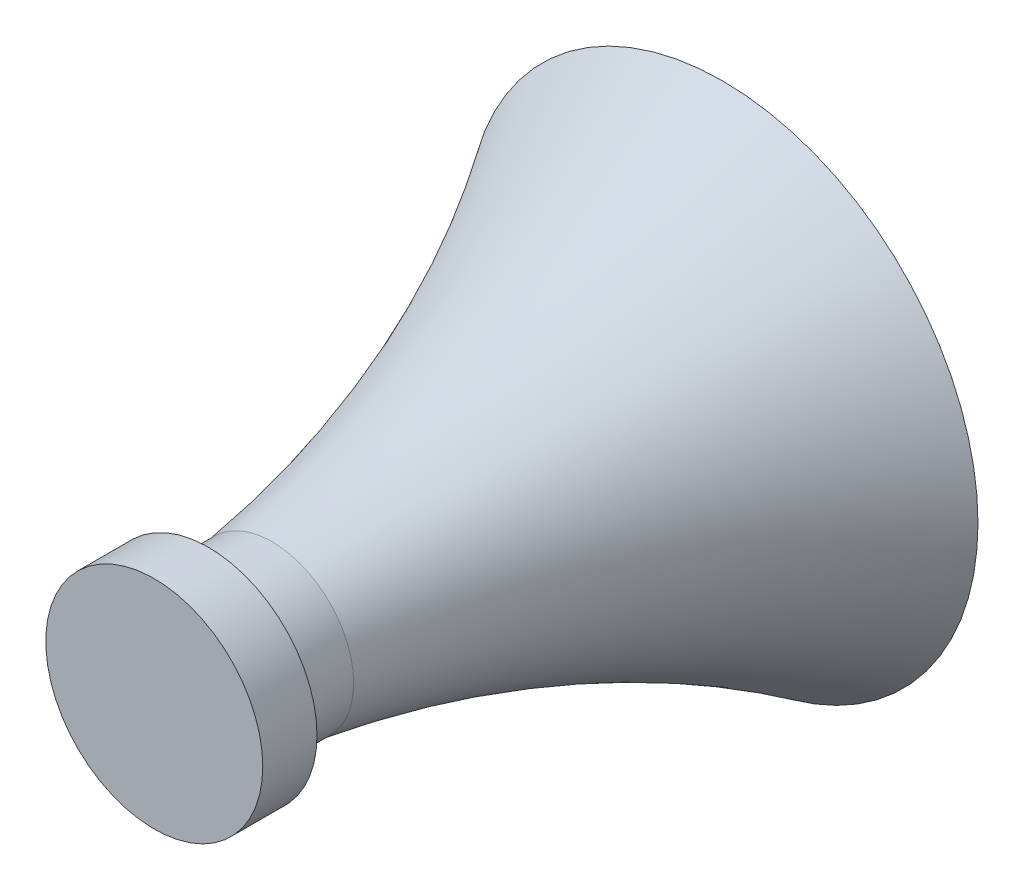
SolidWorks part; units mm, degrees
ref_plane "Front Plane" through (0, 0, 0) normal (0, 0, 1) x (1, 0, 0)
ref_plane "Top Plane" through (0, 0, 0) normal (0, 1, 0) x (1, 0, 0)
ref_plane "Right Plane" through (0, 0, 0) normal (1, 0, 0) x (0, 0, -1)
sketch "Sketch1" plane through (0, 0, 0) normal (0, 1, 0) x (1, 0, 0)
  line L0 (3.005, 2.3456) -> (3.005, 0)
  line L1 (0, 10) -> (0.75, 10)
  line L2 (0, 0) -> (0, -2)
  line L6 (0, 0) -> (0, 10)
  line L8 (4, 0) -> (4, -2)
  line L9 (4, -2) -> (0, -2)
  line L10 (0, -2) -> (0, 0.7552)
  line L11 (3.005, 0) -> (4, 0)
  line L12 (8.8133, 18.9545) -> (9.4156, 18.9545)
  line L13 (0, -2) -> (0, 16.5535) construction
  arc A0 (2.5, 2.3456) -> (8.8133, 18.9545) centre (42.1127, -3.2074) cw
  arc A1 (0.75, 10) -> (2.5, 2.3456) centre (-43.1982, -4.0749) cw
  arc A3 (9.4156, 18.9545) -> (3.005, 2.3456) centre (42.1127, -3.2074) ccw
  dimension "D2" = 40
  dimension "D3" = 79
  dimension "D1" = 0.75
  dimension "D4" = 2.5
  dimension "D5" = 10
  dimension "D6" = 4
  dimension "D7" = 2
revolve "Revolve2" add sketch "Sketch1" angle 360 about L13
